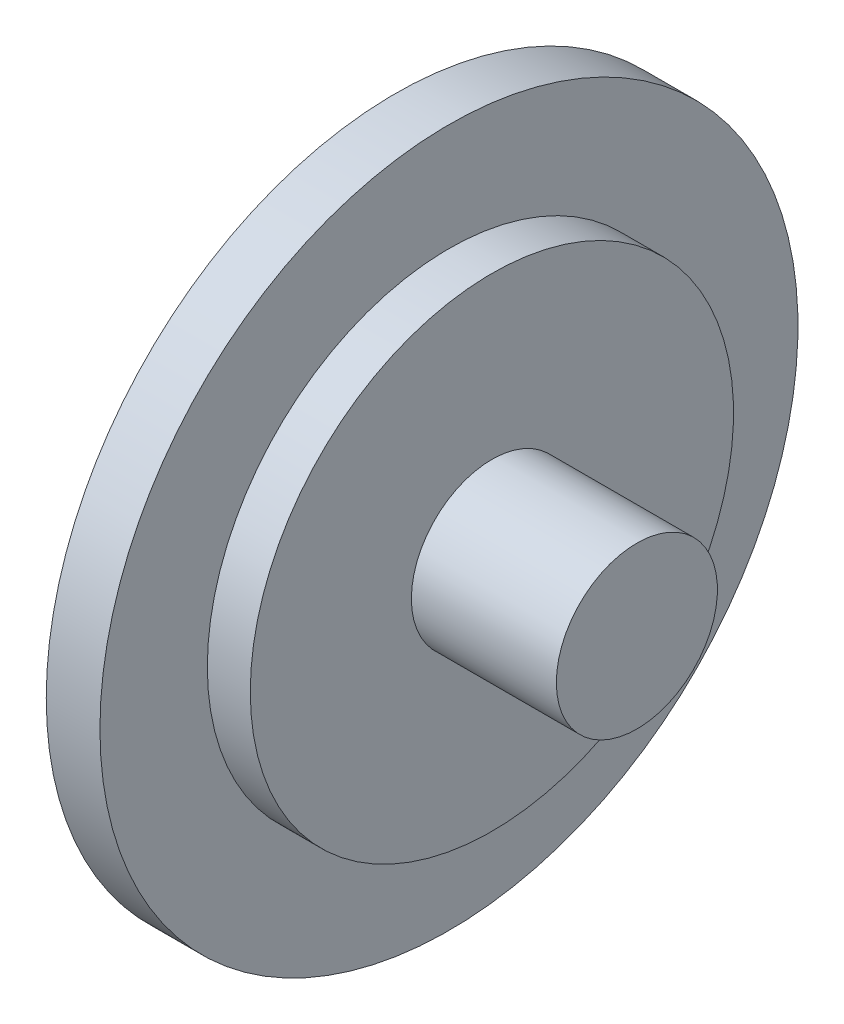
SolidWorks part; units mm, degrees
ref_plane "Front" through (0, 0, 0) normal (0, 0, 1) x (1, 0, 0)
ref_plane "Top" through (0, 0, 0) normal (0, 1, 0) x (1, 0, 0)
ref_plane "Right" through (0, 0, 0) normal (1, 0, 0) x (0, 0, -1)
sketch "Sketch1" plane through (0, 0, 0) normal (0, 0, 1) x (1, 0, 0)
  line L0 (0, 0) -> (0, 13)
  line L1 (0, 13) -> (2, 13)
  line L2 (2, 13) -> (2, 9)
  line L3 (2, 9) -> (3.6, 9)
  line L4 (3.6, 9) -> (3.6, 3)
  line L5 (3.6, 3) -> (9, 3)
  line L6 (9, 3) -> (9, 0)
  line L7 (9, 0) -> (0, 0)
  line L8 (0, 0) -> (28.9286, 0) construction
  dimension "D1" = 2
  dimension "D2" = 26
  dimension "D3" = 6
  dimension "D4" = 3.6
  dimension "D5" = 18
  dimension "D6" = 9
revolve "Revolve1" add sketch "Sketch1" angle 360 about L8
